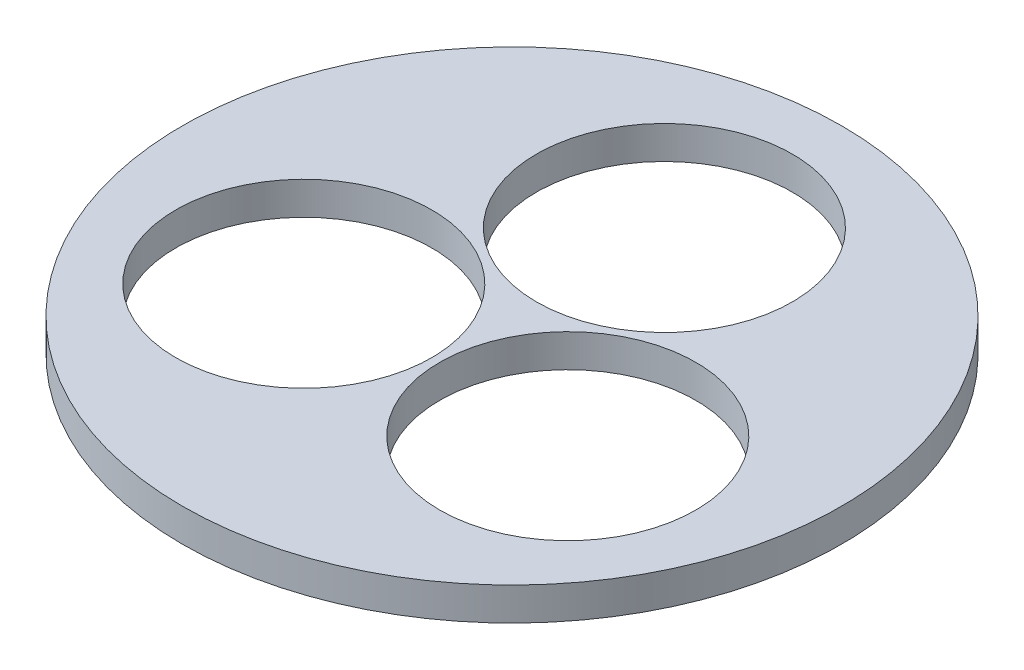
SolidWorks part; units mm, degrees
ref_plane "Front Plane" through (0, 0, 0) normal (0, 0, 1) x (1, 0, 0)
ref_plane "Top Plane" through (0, 0, 0) normal (0, 1, 0) x (1, 0, 0)
ref_plane "Right Plane" through (0, 0, 0) normal (1, 0, 0) x (0, 0, -1)
sketch "Sketch1" plane through (0, 0, 0) normal (0, 1, 0) x (1, 0, 0)
  circle A0 centre (0, 0) radius 101.6
extrude "Boss-Extrude1" add sketch "Sketch1" along normal blind 10.16
sketch "Sketch2" plane through (0, 10.16, 0) normal (0, 1, 0) x (1, 0, 0)
  circle A0 centre (0, 46.99) radius 39.4716
  circle A1 centre (40.6945, -23.495) radius 39.4716
  circle A2 centre (-40.6945, -23.495) radius 39.4716
  point P9 (0, 0)
  dimension "D1" = 3
extrude "Cut-Extrude1" cut sketch "Sketch2" against normal through all
